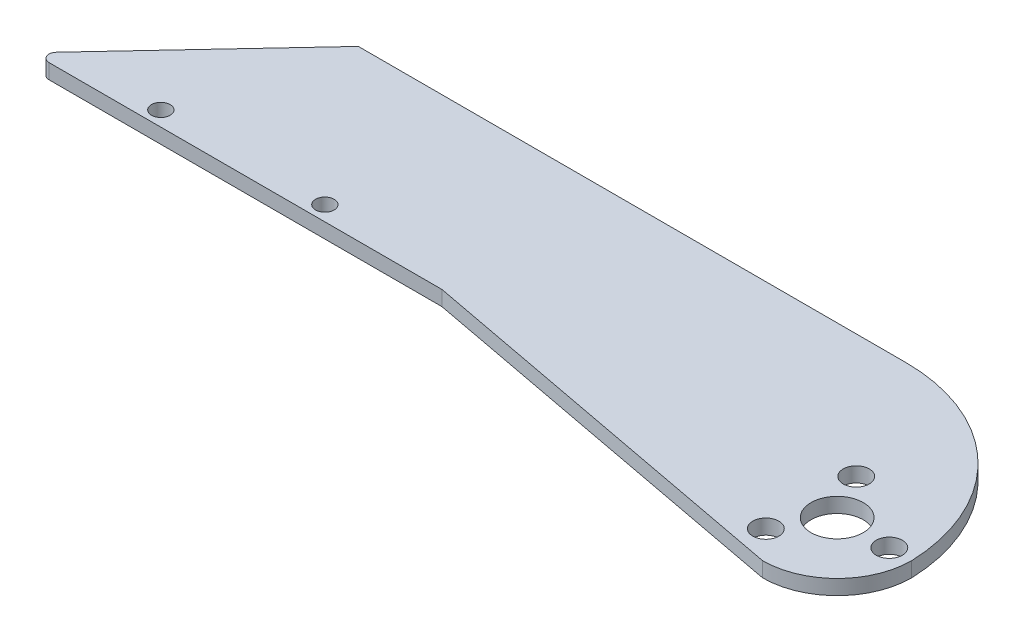
SolidWorks part; units mm, degrees
ref_plane "Спереди" through (0, 0, 0) normal (0, 0, 1) x (1, 0, 0)
ref_plane "Сверху" through (0, 0, 0) normal (0, 1, 0) x (1, 0, 0)
ref_plane "Справа" through (0, 0, 0) normal (1, 0, 0) x (0, 0, -1)
sketch "Sketch1" plane through (0, 0, 0) normal (0, 1, 0) x (1, 0, 0)
  line L0 (-70.2213, 22.6229) -> (-13.4267, 22.6229)
  line L1 (-108, 0) -> (0, 0)
  line L2 (0, -10) -> (0, 10)
  line L3 (-102.9617, -0.614) -> (-80.9617, -0.614) construction
  line L4 (-102.9617, -0.614) -> (-102.9617, 5.386) construction
  line L5 (-108, 0) -> (-86.8374, 22.6229)
  line L6 (-86.8374, 22.6229) -> (-70.2213, 22.6229)
  line L8 (0, -10) -> (-53, 0)
  line L9 (-102.9617, 5.386) -> (-80.9617, 5.386) construction
  line L10 (-80.9617, -0.614) -> (-80.9617, 5.386) construction
  line L13 (-80.9617, 5.386) -> (-59.7052, 5.386) construction
  line L14 (-80.9617, 5.386) -> (-80.9617, -16.7229) construction
  line L15 (-80.9617, -16.7229) -> (-59.7052, -16.7229) construction
  line L16 (-59.7052, 5.386) -> (-59.7052, -16.7229) construction
  circle A0 centre (0, 0) radius 10 construction
  circle A1 centre (-92.7052, 2) radius 1.25
  circle A2 centre (-70.7052, 2) radius 1.25
  circle A3 centre (0, 0) radius 7 construction
  circle A4 centre (7, 0) radius 1.75
  circle A5 centre (-3.5, -6.0622) radius 1.75
  circle A6 centre (-3.5, 6.0622) radius 1.75
  circle A7 centre (0, 0) radius 3.5
  arc A8 (0, -10) -> (0, 10) centre (0, 0) ccw
  arc A9 (-13.4267, 22.6229) -> (10, 0) centre (-13.4267, -0.8181) cw
  arc A10 (0, -10) -> (10, 0) centre (0, 0) ccw
  point P23 (0, 0)
  point P29 (-102.9617, 2.386)
  point P30 (-59.7052, -5.6685)
  point P33 (0, 0)
  dimension "D1" = 20
  dimension "D3" = 22
  dimension "D5" = 2.5
  dimension "D6" = 3
  dimension "D7" = 14
  dimension "D8" = 3.5
  dimension "D9" = 7
  dimension "D10" = 44
  dimension "D13" = 2.5
  dimension "D2" = 108
  dimension "D4" = 53
  dimension "D11" = 2
extrude "Boss-Extrude1" add sketch "Sketch1" along normal blind 2
fillet "Скругление1" radius 1 1 edges at (-108, 1, 0)
